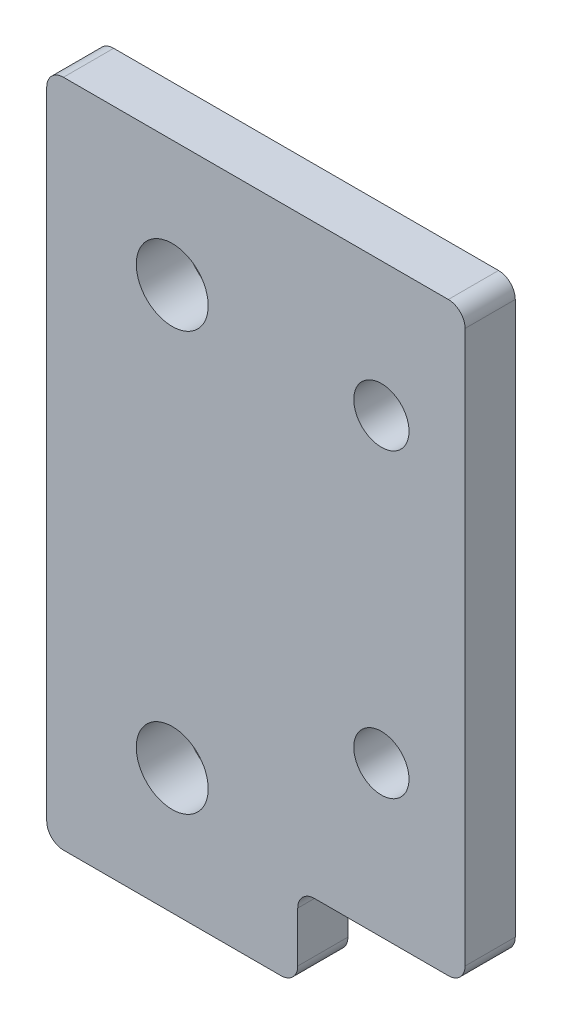
SolidWorks part; units mm, degrees
material "A-玻璃纤维"
ref_plane "前视基准面" through (0, 0, 0) normal (0, 0, 1) x (1, 0, 0)
ref_plane "上视基准面" through (0, 0, 0) normal (0, 1, 0) x (1, 0, 0)
ref_plane "右视基准面" through (0, 0, 0) normal (1, 0, 0) x (0, 0, -1)
sketch "草图1" plane through (0, 0, 0) normal (0, 0, 1) x (1, 0, 0)
  line L0 (0, 0) -> (0, 25) construction
  line L1 (7.5, 32.5) -> (17.5, 32.5)
  line L2 (-7.5, 32.5) -> (7.5, 32.5)
  line L3 (-7.5, 32.5) -> (-7.5, -7.5)
  line L4 (-7.5, -7.5) -> (7.5, -7.5)
  line L5 (7.5, 32.5) -> (7.5, -7.5) construction
  line L6 (-7.5, 32.5) -> (7.5, -7.5) construction
  line L7 (-7.5, -7.5) -> (7.5, 32.5) construction
  line L8 (17.5, 32.5) -> (17.5, -2.5)
  line L9 (17.5, -2.5) -> (7.5, -2.5)
  line L10 (7.5, -7.5) -> (7.5, -2.5)
  line L11 (12.5, 32.5) -> (12.5, -2.5) construction
  circle A0 centre (0, 0) radius 2.15
  circle A1 centre (0, 25) radius 2.15
  circle A2 centre (12.5, 24.5) radius 1.65
  circle A3 centre (12.5, 6.5) radius 1.65
  point P5 (0, 12.5)
  point P19 (12.5, 29.5)
  dimension "D1" = 4.3
  dimension "D2" = 25
  dimension "D7" = 3.3
  dimension "D8" = 8
  dimension "D9" = 18
  dimension "D3" = 15
  dimension "D4" = 40
  dimension "D5" = 35
  dimension "D6" = 10
extrude "凸台-拉伸1" add sketch "草图1" along normal blind 3
fillet "圆角1" radius 1 6 edges at (7.5, -7.5, 1.5) (-7.5, -7.5, 1.5) (-7.5, 32.5, 1.5) (17.5, 32.5, 1.5) (17.5, -2.5, 1.5) (7.5, -2.5, 1.5)
